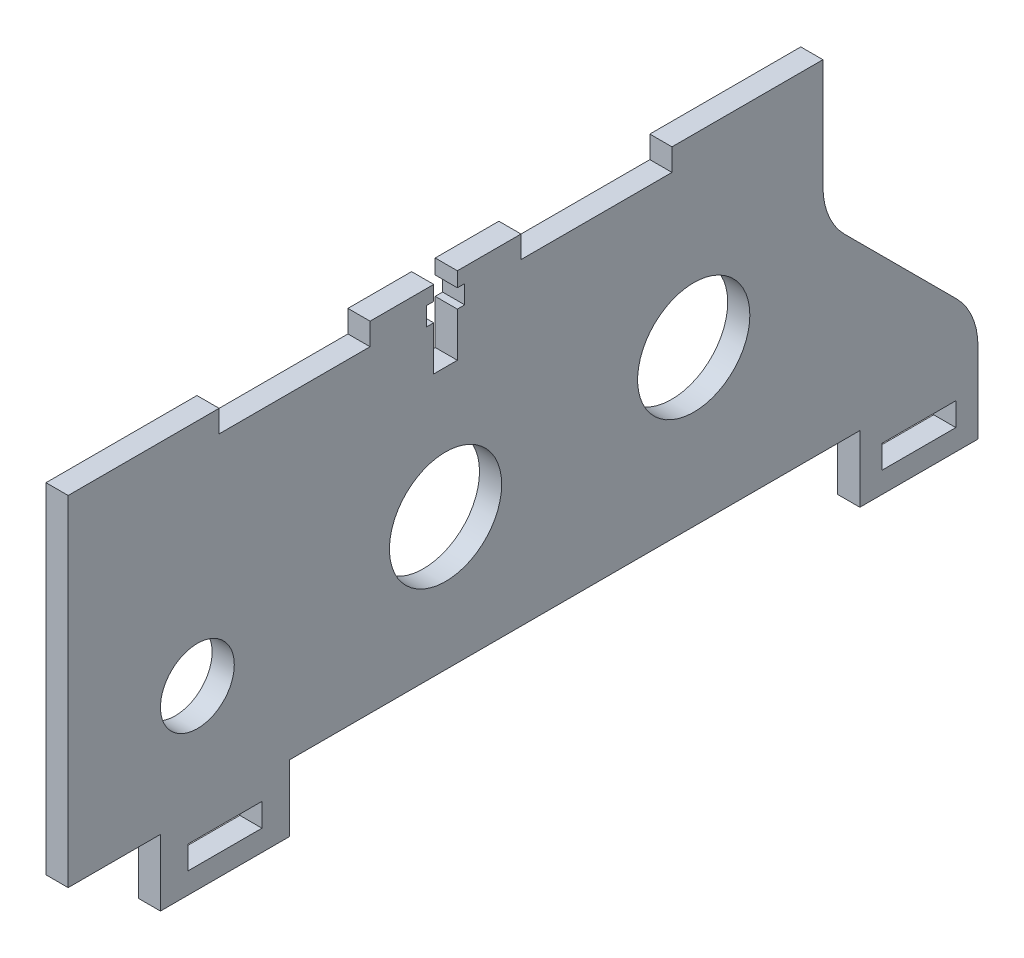
SolidWorks part; units mm, degrees
ref_plane "Front Plane" through (0, 0, 0) normal (0, 0, 1) x (1, 0, 0)
ref_plane "Top Plane" through (0, 0, 0) normal (0, 1, 0) x (1, 0, 0)
ref_plane "Right Plane" through (0, 0, 0) normal (1, 0, 0) x (0, 0, -1)
sketch "Sketch1" plane through (0, 0, 0) normal (1, 0, 0) x (0, 0, -1)
  line L0 (0, 0) -> (0, 46)
  line L3 (123.2238, -9) -> (107.2238, -9)
  line L4 (107.2238, -9) -> (107.2238, 0)
  line L9 (107.2238, 0) -> (30, 0)
  line L12 (0, 0) -> (12.5, 0)
  line L17 (12.5, 0) -> (12.5, -9)
  line L18 (12.5, -9) -> (30, -9)
  line L19 (30, -9) -> (30, 0)
  line L20 (0, 46) -> (20.4448, 46)
  line L21 (20.4448, 46) -> (20.4448, 43)
  line L22 (20.4448, 43) -> (40.8895, 43)
  line L23 (40.8895, 43) -> (40.8895, 46)
  line L24 (40.8895, 46) -> (61.3343, 46)
  line L25 (61.3343, 46) -> (61.3343, 43)
  line L26 (61.3343, 43) -> (81.779, 43)
  line L27 (81.779, 43) -> (81.779, 46)
  line L28 (81.779, 46) -> (102.2238, 46)
  line L29 (17.5, 14.9) -> (84.7238, 21) construction
  line L30 (102.2238, 46) -> (102.2238, 6)
  line L32 (123.2238, 6) -> (123.2238, -9)
  line L37 (102.2238, 6) -> (123.2238, 6)
  line L40 (102.2238, 27) -> (123.2238, 6)
  line L41 (16.25, -6.15) -> (26.25, -6.15)
  line L42 (16.25, -6.15) -> (16.25, -3)
  line L43 (16.25, -3) -> (26.25, -3)
  line L44 (26.25, -6.15) -> (26.25, -3)
  line L45 (16.25, -6.15) -> (26.25, -3) construction
  line L46 (16.25, -3) -> (26.25, -6.15) construction
  line L47 (110.2238, -6.15) -> (120.2238, -6.15)
  line L48 (110.2238, -6.15) -> (110.2238, -3)
  line L49 (110.2238, -3) -> (120.2238, -3)
  line L50 (120.2238, -6.15) -> (120.2238, -3)
  line L51 (110.2238, -6.15) -> (120.2238, -3) construction
  line L52 (110.2238, -3) -> (120.2238, -6.15) construction
  circle A0 centre (17.5, 14.9) radius 5
  circle A1 centre (51.1119, 17.95) radius 7.6
  circle A2 centre (84.7238, 21) radius 7.6
  point P9 (115.2238, -4.575)
  point P14 (21.25, -4.575)
  point P20 (21.25, -9)
  point P21 (115.2238, -9)
  point P37 (51.1119, 17.95)
  point P41 (17.5, 14.9)
  point P42 (51.1119, 17.95)
  point P43 (84.7238, 21)
  dimension "D10" = 10
  dimension "D11" = 15.2
  dimension "D2" = 46
  dimension "D3" = 9
  dimension "D4" = 14.9
  dimension "D5" = 67.5
  dimension "D6" = 17.5
  dimension "D7" = 17.5
  dimension "D8" = 21
  dimension "D9" = 3
  dimension "D12" = 5
  dimension "D13" = 16
  dimension "D14" = 15
  dimension "D15" = 17.5
  dimension "D16" = 3
  dimension "D17" = 10
  dimension "D18" = 3.15
  dimension "D19" = 12.5
  dimension "D20" = 45
extrude "Boss-Extrude1" add sketch "Sketch1" along normal blind 3 contours L40 L30 L37 | L37 L30 L28 L27 L26 L25 L24 L23 L22 L21 L20 L0 L12 L17 L18 L19 L9 L4 L3 L32 A2 A1 A0 L50 L47 L48 L49 L44 L41 L42 L43
fillet "Fillet1" radius 10 2 edges at (1.5, 6, -123.2238) (1.5, 27, -102.2238)
sketch "Sketch2" plane through (3, 0, 0) normal (1, 0, 0) x (0, 0, -1)
  line L0 (40.8895, 46) -> (61.3343, 46) construction
  line L1 (48.5119, 41.5) -> (53.7119, 41.5)
  line L2 (48.5119, 41.5) -> (48.5119, 44)
  line L3 (48.5119, 44) -> (53.7119, 44)
  line L4 (53.7119, 41.5) -> (53.7119, 44)
  line L5 (48.5119, 41.5) -> (53.7119, 44) construction
  line L6 (48.5119, 44) -> (53.7119, 41.5) construction
  line L7 (49.5119, 46) -> (52.7119, 46)
  line L8 (49.5119, 46) -> (49.5119, 35.5)
  line L9 (49.5119, 35.5) -> (52.7119, 35.5)
  line L10 (52.7119, 46) -> (52.7119, 35.5)
  line L11 (49.5119, 46) -> (52.7119, 35.5) construction
  line L12 (49.5119, 35.5) -> (52.7119, 46) construction
  point P0 (51.1119, 42.75)
  point P5 (51.1119, 40.75)
  point P13 (51.1119, 46)
  line M15 (61.3343, 46) -> (40.8895, 46)
  dimension "D1" = 10.5
  dimension "D2" = 3.2
  dimension "D3" = 5.2
  dimension "D4" = 2
  dimension "D5" = 2.5
extrude "Cut-Extrude1" cut sketch "Sketch2" against normal through all both and the other way through all contours L10 L1 L8 L9 | L10 L3 L8 L1 | L8 L3 L2 L1 | L10 L8 L3 M15 | L3 L10 L1 L4
